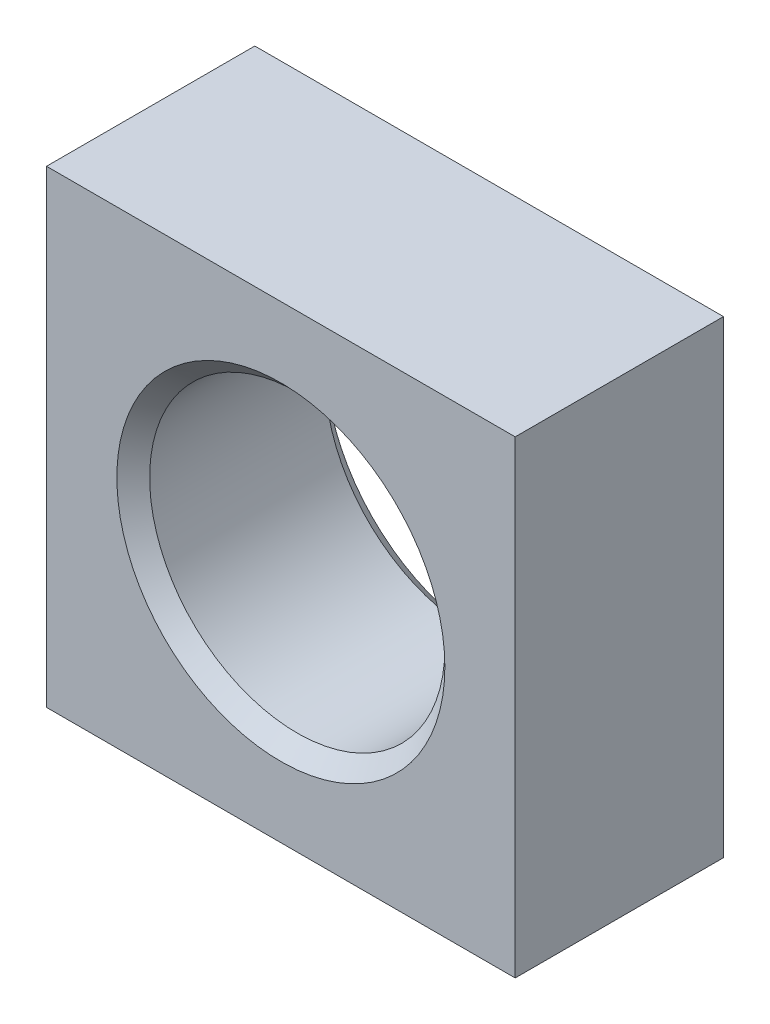
SolidWorks part; units mm, degrees
material "6061-T6 Al"
ref_plane "Front" through (0, 0, 0) normal (0, 0, 1) x (1, 0, 0)
ref_plane "Top" through (0, 0, 0) normal (0, 1, 0) x (1, 0, 0)
ref_plane "Right" through (0, 0, 0) normal (1, 0, 0) x (0, 0, -1)
sketch "Sketch" plane through (0, 0, 0) normal (0, 0, 1) x (1, 0, 0)
  line L2 (14.2875, 14.2875) -> (-14.2875, -14.2875) construction
  line L3 (14.2875, 14.2875) -> (-14.2875, 14.2875)
  line L4 (14.2875, 14.2875) -> (14.2875, -14.2875)
  line L6 (14.2875, -14.2875) -> (-14.2875, -14.2875)
  line L7 (-14.2875, 14.2875) -> (-14.2875, -14.2875)
  point P5 (-25.908, 20.828)
  point P6 (25.908, 20.828)
  point P7 (25.908, -20.828)
  point P8 (-25.908, -20.828)
  point P63 (-25.781, -19.05)
  point P64 (25.781, -19.05)
  dimension "D1" = 28.575
extrude "Boss-Extrude1" add sketch "Sketch" against normal blind 12.7
hole_wizard "M20x2.0 Tapped Hole1" positions "Sketch2" profile "Sketch1" tap size "M20x2.0" standard "ANSI Metric" end condition through all
sketch "Sketch2" plane through (0, 0, 0) normal (0, 0, 1) x (1, 0, 0)
  point P0 (0, 0)
sketch "Sketch1" plane through (0, 0, 0) normal (1, 0, 0) x (0, -1, 0)
  line L0 (0, 0) -> (0, 12.7)
  line L1 (0, 12.7) -> (10, 12.7)
  line L2 (9, 11.7) -> (9, 1)
  line L3 (9, 1) -> (10, 0)
  line L5 (10, 0) -> (0, 0)
  line L6 (-9, 1) -> (-10, 0) construction
  line L7 (10, 12.7) -> (9, 11.7)
  line L8 (-10, 12.7) -> (-9, 11.7) construction
  line L11 (0, -6.35) -> (0, 107.95) construction
  dimension "Thru Tap Drill Dia." = 18
  dimension "Thru Tap Drill Depth" = 12.7
  dimension "Near C'Sink Dia." = 20
  dimension "Near C'Sink Angle" = 90
  dimension "Far C'Sink Dia." = 20
  dimension "Far C'Sink Angle" = 90
cosmetic thread "Hole Thread1" parameters "D2"=20
